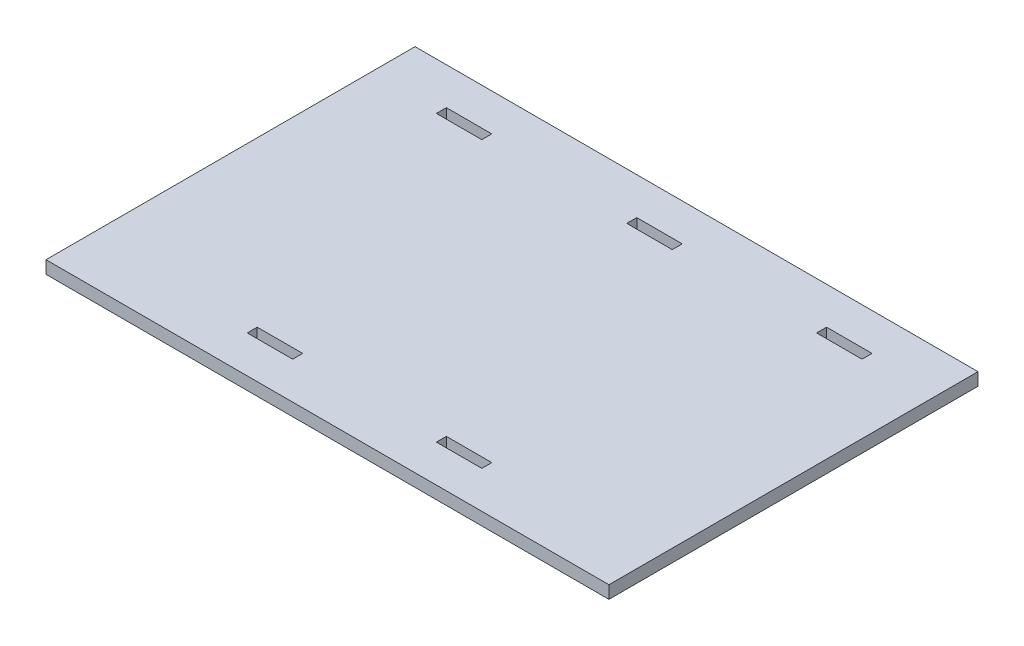
SolidWorks part; units mm, degrees
ref_plane "Front Plane" through (0, 0, 0) normal (0, 0, 1) x (1, 0, 0)
ref_plane "Top Plane" through (0, 0, 0) normal (0, 1, 0) x (1, 0, 0)
ref_plane "Right Plane" through (0, 0, 0) normal (1, 0, 0) x (0, 0, -1)
sketch "Sketch2" plane through (0, 0, 0) normal (0, 1, 0) x (1, 0, 0)
  line L1 (-281.815, -184.75) -> (281.815, -184.75)
  line L2 (-281.815, -184.75) -> (-281.815, 184.75)
  line L3 (-281.815, 184.75) -> (281.815, 184.75)
  line L4 (281.815, -184.75) -> (281.815, 184.75)
  line L5 (-281.815, -184.75) -> (281.815, 184.75) construction
  line L6 (-281.815, 184.75) -> (281.815, -184.75) construction
  point P0 (0, 0)
  dimension "D1" = 369.5
  dimension "D2" = 563.63
extrude "Boss-Extrude1" add sketch "Sketch2" along normal blind 12.7
sketch "Sketch3" plane through (0, 12.7, 0) normal (0, 1, 0) x (1, 0, 0)
  line L0 (-207.2358, 142.5) -> (-173.0799, 142.5)
  line L1 (-17.2358, 142.5) -> (16.9201, 142.5)
  line L2 (172.7642, 142.5) -> (206.9201, 142.5)
  line L3 (-112.2358, -142.5) -> (-78.0799, -142.5)
  line L4 (77.7642, -142.5) -> (111.9201, -142.5)
  line L6 (-213.2358, 147.5) -> (-167.7358, 147.5)
  line L7 (-213.2358, 147.5) -> (-213.2358, 137.5)
  line L8 (-213.2358, 137.5) -> (-167.7358, 137.5)
  line L9 (-167.7358, 147.5) -> (-167.7358, 137.5)
  line L10 (-22.5799, 147.5) -> (22.9201, 147.5)
  line L11 (-22.5799, 147.5) -> (-22.5799, 137.5)
  line L12 (-22.5799, 137.5) -> (22.9201, 137.5)
  line L13 (22.9201, 147.5) -> (22.9201, 137.5)
  line L14 (167.4201, 147.5) -> (212.9201, 147.5)
  line L15 (167.4201, 147.5) -> (167.4201, 137.5)
  line L16 (167.4201, 137.5) -> (212.9201, 137.5)
  line L17 (212.9201, 147.5) -> (212.9201, 137.5)
  line L18 (71.7642, -137.5) -> (117.2642, -137.5)
  line L19 (71.7642, -137.5) -> (71.7642, -147.5)
  line L20 (71.7642, -147.5) -> (117.2642, -147.5)
  line L21 (117.2642, -137.5) -> (117.2642, -147.5)
  line L22 (-117.5799, -137.5) -> (-72.0799, -137.5)
  line L23 (-117.5799, -137.5) -> (-117.5799, -147.5)
  line L24 (-117.5799, -147.5) -> (-72.0799, -147.5)
  line L25 (-72.0799, -137.5) -> (-72.0799, -147.5)
  point P40 (-167.7358, 142.5)
  point P41 (22.9201, 142.5)
  point P42 (212.9201, 142.5)
  point P43 (117.2642, -142.5)
  point P44 (0, 0)
  point P45 (-72.0799, -142.5)
  dimension "D1" = 10
  dimension "D2" = 10
  dimension "D3" = 10
  dimension "D4" = 10
  dimension "D5" = 10
  dimension "D6" = 45.5
  dimension "D7" = 6
  dimension "D8" = 45.5
  dimension "D9" = 6
  dimension "D10" = 45.5
  dimension "D11" = 6
  dimension "D12" = 45.5
  dimension "D13" = 6
  dimension "D14" = 45.5
  dimension "D15" = 6
extrude "Cut-Extrude2" cut sketch "Sketch3" along normal through all both and the other way through all contours L8 L9 L6 L7 | L12 L13 L10 L11 | L14 L17 L16 L15 | L22 L25 L24 L23 | L18 L21 L20 L19
